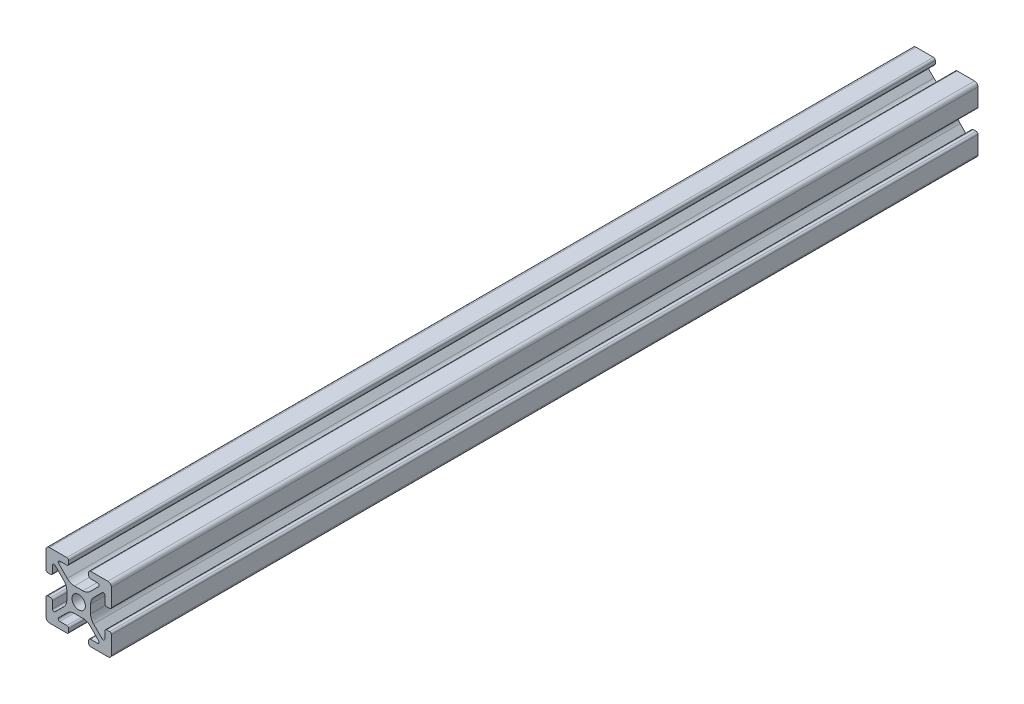
SolidWorks part; units mm, degrees
ref_plane "Front Plane" through (0, 0, 0) normal (0, 0, 1) x (1, 0, 0)
ref_plane "Top Plane" through (0, 0, 0) normal (0, 1, 0) x (1, 0, 0)
ref_plane "Right Plane" through (0, 0, 0) normal (1, 0, 0) x (0, 0, -1)
sketch "Sketch1" plane through (0, 0, 0) normal (0, 0, 1) x (1, 0, 0)
  line L0 (-3.6422, 1.2878) -> (-3.6422, -1.2878)
  line L1 (-1.2878, 3.6422) -> (1.2878, 3.6422)
  line L2 (-9.4433, 3.069) -> (-8.553, 3.069)
  line L3 (0, 0) -> (-15.7854, 0) construction
  line L4 (-3.4964, 4.5571) -> (-6.1213, 7.182)
  line L5 (-3.622, 8) -> (-5.7825, 8)
  line L6 (-3.069, 9.4433) -> (-3.069, 8.553)
  line L7 (-3.622, 10) -> (-8.939, 10)
  line L8 (0, 0) -> (0, 15.0393) construction
  line L9 (10, 3.622) -> (10, 8.939)
  line L10 (8, 3.622) -> (8, 5.7825)
  line L11 (4.5571, 3.4964) -> (7.182, 6.1213)
  line L12 (3.622, 10) -> (8.939, 10)
  line L13 (3.069, 9.4433) -> (3.069, 8.553)
  line L14 (3.622, 8) -> (5.7825, 8)
  line L15 (3.4964, 4.5571) -> (6.1213, 7.182)
  line L16 (9.4433, 3.069) -> (8.553, 3.069)
  line L17 (3.6422, 1.2878) -> (3.6422, -1.2878)
  line L18 (-10, -3.622) -> (-10, -8.939)
  line L19 (-8, -3.622) -> (-8, -5.7825)
  line L20 (-4.5571, -3.4964) -> (-7.182, -6.1213)
  line L21 (9.4433, -3.069) -> (8.553, -3.069)
  line L22 (3.4964, -4.5571) -> (6.1213, -7.182)
  line L23 (3.622, -8) -> (5.7825, -8)
  line L24 (3.069, -9.4433) -> (3.069, -8.553)
  line L25 (3.622, -10) -> (8.939, -10)
  line L26 (4.5571, -3.4964) -> (7.182, -6.1213)
  line L27 (8, -3.622) -> (8, -5.7825)
  line L28 (10, -3.622) -> (10, -8.939)
  line L29 (-3.622, -10) -> (-8.939, -10)
  line L30 (-3.069, -9.4433) -> (-3.069, -8.553)
  line L31 (-3.622, -8) -> (-5.7825, -8)
  line L32 (-3.4964, -4.5571) -> (-6.1213, -7.182)
  line L33 (-9.4433, -3.069) -> (-8.553, -3.069)
  line L34 (-1.2878, -3.6422) -> (1.2878, -3.6422)
  line L48 (-4.5571, 3.4964) -> (-7.182, 6.1213)
  line L49 (-8, 3.622) -> (-8, 5.7825)
  line L52 (-10, 3.622) -> (-10, 8.939)
  arc A0 (-8.553, 3.069) -> (-8, 3.622) centre (-8.553, 3.622) ccw
  arc A1 (-8, 5.7825) -> (-7.182, 6.1213) centre (-7.5208, 5.7825) cw
  arc A2 (-4.5571, 3.4964) -> (-3.6422, 1.2878) centre (-6.7657, 1.2878) cw
  arc A3 (-3.4964, 4.5571) -> (-1.2878, 3.6422) centre (-1.2878, 6.7657) ccw
  arc A4 (-5.7825, 8) -> (-6.1213, 7.182) centre (-5.7825, 7.5208) ccw
  arc A5 (-3.622, 10) -> (-3.069, 9.4433) centre (-3.622, 9.447) cw
  arc A6 (-3.069, 8.553) -> (-3.622, 8) centre (-3.622, 8.553) cw
  arc A7 (8.939, 10) -> (10, 8.939) centre (8.939, 8.939) cw
  arc A8 (10, 3.622) -> (9.4433, 3.069) centre (9.447, 3.622) cw
  arc A9 (3.069, 8.553) -> (3.622, 8) centre (3.622, 8.553) ccw
  arc A10 (3.622, 10) -> (3.069, 9.4433) centre (3.622, 9.447) ccw
  arc A11 (5.7825, 8) -> (6.1213, 7.182) centre (5.7825, 7.5208) cw
  arc A12 (3.4964, 4.5571) -> (1.2878, 3.6422) centre (1.2878, 6.7657) cw
  arc A13 (4.5571, 3.4964) -> (3.6422, 1.2878) centre (6.7657, 1.2878) ccw
  arc A14 (8, 5.7825) -> (7.182, 6.1213) centre (7.5208, 5.7825) ccw
  arc A15 (8.553, 3.069) -> (8, 3.622) centre (8.553, 3.622) cw
  arc A16 (-8.939, -10) -> (-10, -8.939) centre (-8.939, -8.939) cw
  arc A17 (-10, -3.622) -> (-9.4433, -3.069) centre (-9.447, -3.622) cw
  arc A18 (8.553, -3.069) -> (8, -3.622) centre (8.553, -3.622) ccw
  arc A19 (8, -5.7825) -> (7.182, -6.1213) centre (7.5208, -5.7825) cw
  arc A20 (4.5571, -3.4964) -> (3.6422, -1.2878) centre (6.7657, -1.2878) cw
  arc A21 (3.4964, -4.5571) -> (1.2878, -3.6422) centre (1.2878, -6.7657) ccw
  arc A22 (5.7825, -8) -> (6.1213, -7.182) centre (5.7825, -7.5208) ccw
  arc A23 (3.622, -10) -> (3.069, -9.4433) centre (3.622, -9.447) cw
  arc A24 (3.069, -8.553) -> (3.622, -8) centre (3.622, -8.553) cw
  arc A25 (10, -3.622) -> (9.4433, -3.069) centre (9.447, -3.622) ccw
  arc A26 (8.939, -10) -> (10, -8.939) centre (8.939, -8.939) ccw
  arc A27 (-3.069, -8.553) -> (-3.622, -8) centre (-3.622, -8.553) ccw
  arc A28 (-3.622, -10) -> (-3.069, -9.4433) centre (-3.622, -9.447) ccw
  arc A29 (-5.7825, -8) -> (-6.1213, -7.182) centre (-5.7825, -7.5208) cw
  arc A30 (-3.4964, -4.5571) -> (-1.2878, -3.6422) centre (-1.2878, -6.7657) cw
  arc A31 (-4.5571, -3.4964) -> (-3.6422, -1.2878) centre (-6.7657, -1.2878) ccw
  arc A32 (-8, -5.7825) -> (-7.182, -6.1213) centre (-7.5208, -5.7825) ccw
  arc A33 (-8.553, -3.069) -> (-8, -3.622) centre (-8.553, -3.622) cw
  arc A51 (-10, 3.622) -> (-9.4433, 3.069) centre (-9.447, 3.622) ccw
  arc A56 (-8.939, 10) -> (-10, 8.939) centre (-8.939, 8.939) ccw
  circle A57 centre (0, 0) radius 2.05
  point P1 (-3.6422, 0)
  point P46 (0, 0)
  point P48 (0, 0)
  point P53 (0, 3.6422)
  point P60 (0, 0)
  point P61 (0, 0)
  point P62 (0, 0)
  point P74 (0, 0)
  point P85 (0, 0)
  point P87 (0, 0)
  point P99 (0, 0)
  point P101 (0, 0)
  point P102 (0, 0)
  point P116 (0, -3.6422)
  point P117 (3.6422, 0)
  point P123 (0, 0)
  point P125 (0, 0)
  point P127 (0, 0)
  point P139 (0, 0)
  point P140 (0, 0)
  point P141 (0, 0)
  point P142 (0, 0)
  point P179 (0, 0)
  point P192 (0, 0)
  point P193 (0, 0)
  dimension "D1" = 0.553
  dimension "D3" = 3.1235
  dimension "D4" = 0.553
  dimension "D2" = 0.4792
  dimension "D9" = 3.4964
  dimension "D10" = 3.6422
  dimension "D11" = 4.5571
  dimension "D12" = 5.7825
  dimension "D13" = 9.4433
  dimension "D5" = 1.061
  dimension "D6" = 2.05
  dimension "D7" = 1.2878
  dimension "D8" = 3.069
extrude "Boss-Extrude1" add sketch "Sketch1" against normal blind 265
